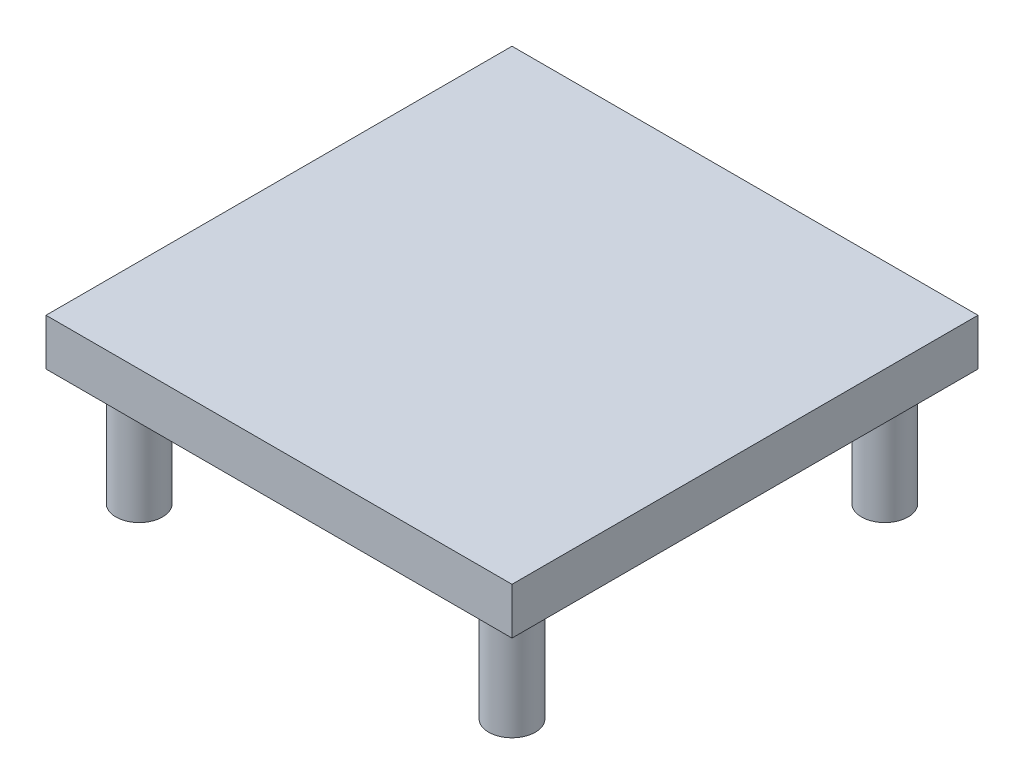
SolidWorks part; units mm, degrees
ref_plane "Front Plane" through (0, 0, 0) normal (0, 0, 1) x (1, 0, 0)
ref_plane "Top Plane" through (0, 0, 0) normal (0, 1, 0) x (1, 0, 0)
ref_plane "Right Plane" through (0, 0, 0) normal (1, 0, 0) x (0, 0, -1)
sketch "Sketch1" plane through (0, 0, 0) normal (0, 1, 0) x (1, 0, 0)
  line L1 (100, 100) -> (-100, 100)
  line L2 (-100, 100) -> (-100, -100)
  line L3 (-100, -100) -> (100, -100)
  line L4 (100, -100) -> (100, 100)
  circle A0 centre (0, 0) radius 100 construction
extrude "Boss-Extrude1" add sketch "Sketch1" along normal blind 20
sketch "Sketch2" plane through (0, 0, 0) normal (0, -1, 0) x (1, 0, 0)
  line L1 (-100, 100) -> (100, 100) construction
  line L2 (100, 100) -> (100, -100) construction
  circle A0 centre (80, 80) radius 10
  circle A1 centre (80, -80) radius 10
  circle A2 centre (-80, -80) radius 10
  circle A3 centre (-80, 80) radius 10
  point P16 (0, 0)
  dimension "D1" = 20
  dimension "D2" = 20
  dimension "D3" = 4
extrude "Boss-Extrude2" add sketch "Sketch2" along normal blind 50
